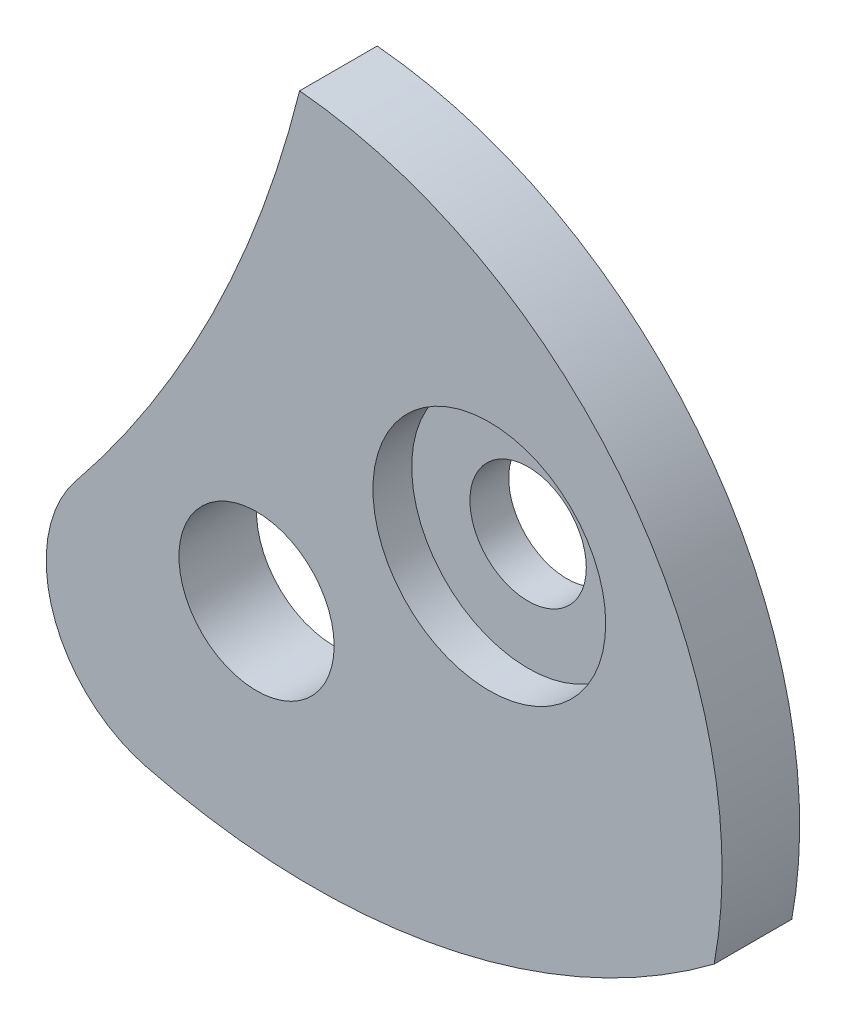
SolidWorks part; units mm, degrees
ref_plane "Alzado" through (0, 0, 0) normal (0, 0, 1) x (1, 0, 0)
ref_plane "Planta" through (0, 0, 0) normal (0, 1, 0) x (1, 0, 0)
ref_plane "Vista lateral" through (0, 0, 0) normal (1, 0, 0) x (0, 0, -1)
sketch "Croquis1" plane through (0, 0, 0) normal (0, 0, 1) x (1, 0, 0)
  arc A0 (2.949, -0.5507) -> (0.2776, 2.9871) centre (0, 0) ccw
  arc A1 (-1.1654, 0.0875) -> (0.2776, 2.9871) centre (-7, 4.8) ccw
  arc A2 (-1.1654, 0.0875) -> (-0.7124, -1.2786) centre (-0.5, -0.45) ccw
  arc A3 (-0.7124, -1.2786) -> (2.949, -0.5507) centre (0.3594, 2.903) ccw
  circle A4 centre (0, 0) radius 0.5
extrude "Saliente-Extruir1" add sketch "Croquis1" along normal blind 0.5
sketch "Croquis2" plane through (0, 0, 0.5) normal (0, 0, 1) x (1, 0, 0)
  circle A0 centre (1.5, 1) radius 0.75
  dimension "D1" = 1.5
  dimension "D2" = 1.5
  dimension "D3" = 1
extrude "Cortar-Extruir1" cut sketch "Croquis2" against normal blind 0.25
hole_wizard "Taladro roscado M1x0.251" positions "Croquis4" profile "Croquis3" tap size "M1x0.25" standard "KS" end condition through all
sketch "Croquis4" plane through (0, 0, 0.25) normal (0, 0, 1) x (1, 0, 0)
  circle A0 centre (1.5, 1) radius 0.75 construction
  point P0 (1.5, 1)
sketch "Croquis3" plane through (1.5, 1, 0.25) normal (1, 0, 0) x (0, -1, 0)
  line L0 (0, 0) -> (0, 0.25)
  line L1 (0, 0.25) -> (0.375, 0.25)
  line L2 (0.375, 0.25) -> (0.375, 0)
  line L5 (0.375, 0) -> (0, 0)
  line L11 (0, -6.35) -> (0, 107.95) construction
  dimension "Diámetro de perforador para roscar hasta el siguiente" = 0.75
  dimension "Profundidad de perforador para roscar hasta el siguiente" = 0.25
cosmetic thread "Rosca de taladro1" parameters "D2"=1
